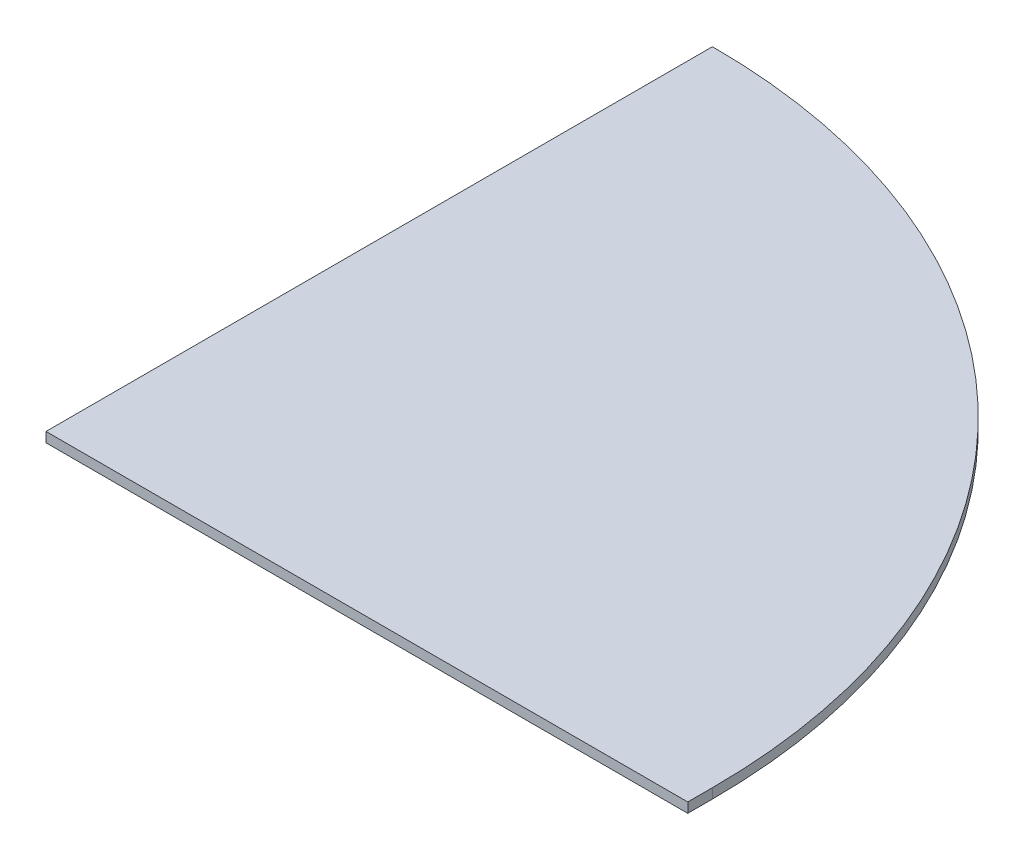
SolidWorks part; units mm, degrees
ref_plane "Front Plane" through (0, 0, 0) normal (0, 0, 1) x (1, 0, 0)
ref_plane "Top Plane" through (0, 0, 0) normal (0, 1, 0) x (1, 0, 0)
ref_plane "Right Plane" through (0, 0, 0) normal (1, 0, 0) x (0, 0, -1)
sketch "Sketch2" plane through (0, 0, 0) normal (0, 1, 0) x (1, 0, 0)
  line L0 (660.4, 0) -> (0, 0)
  line L1 (0, 660.4) -> (0, -25.4)
  line L2 (660.4, 0) -> (0, 0)
  line L3 (660.4, 0) -> (660.4, -25.4)
  line L4 (660.4, -25.4) -> (0, -25.4)
  arc A0 (660.4, 0) -> (0, 660.4) centre (0, 0) ccw
  dimension "D1" = 1320.8
  dimension "D2" = 25.4
extrude "Boss-Extrude1" add sketch "Sketch2" along normal blind 10.16
